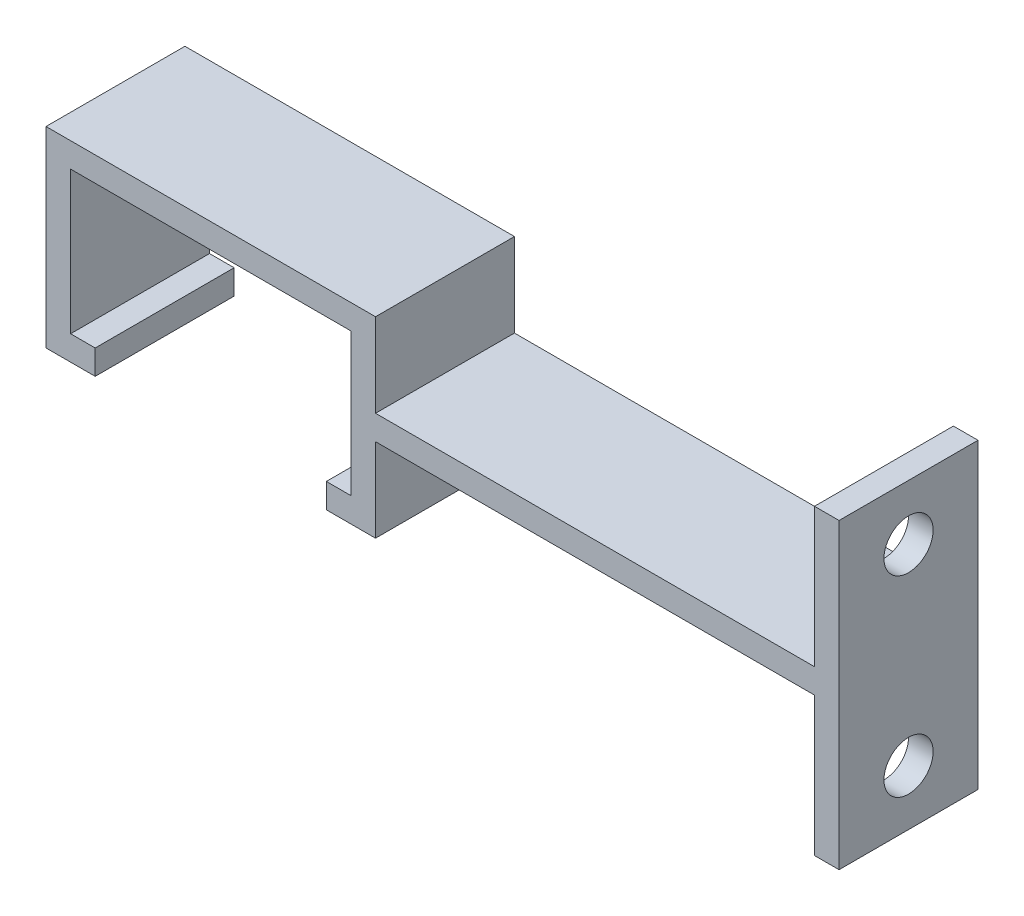
SolidWorks part; units mm, degrees
material "PLA"
ref_plane "Plan de face" through (0, 0, 0) normal (0, 0, 1) x (1, 0, 0)
ref_plane "Plan de dessus" through (0, 0, 0) normal (0, 1, 0) x (1, 0, 0)
ref_plane "Plan de droite" through (0, 0, 0) normal (1, 0, 0) x (0, 0, -1)
sketch "Esquisse1" plane through (0, 0, 0) normal (0, 0, 1) x (1, 0, 0)
  line L0 (-21.8, 1) -> (-21.8, 0)
  line L1 (0, 0) -> (-3, 0)
  line L2 (0, 0) -> (0, 13.6)
  line L3 (0, 13.6) -> (-24.8, 13.6)
  line L4 (-24.8, 0) -> (-24.8, 13.6)
  line L5 (-23.8, 12.6) -> (-1, 12.6)
  line L6 (-23.8, 12.6) -> (-23.8, 1)
  line L7 (-23.8, 1) -> (-21.8, 1)
  line L8 (-1, 12.6) -> (-1, 1)
  line L9 (-3, 1) -> (-3, 0)
  line L10 (-3, 1) -> (-1, 1)
  line L11 (-21.8, 0) -> (-24.8, 0)
  dimension "D1" = 13.6
  dimension "D2" = 24.8
  dimension "D3" = 1
  dimension "D4" = 1
  dimension "D5" = 1
  dimension "D6" = 1
  dimension "D7" = 3
  dimension "D8" = 3
extrude "Boss.-Extru.1" add sketch "Esquisse1" along normal blind 11.3
sketch "Esquisse2" plane through (0, 13.6, 0) normal (0, 1, 0) x (1, 0, 0)
  line L0 (0, -11.3) -> (-24.8, -11.3) construction
  line L1 (-16.8, 0) -> (-8, 0)
  line L2 (-16.8, 0) -> (-16.8, -11.3)
  line L3 (-16.8, -11.3) -> (-8, -11.3)
  line L4 (-8, 0) -> (-8, -11.3)
  line L5 (-24.8, -11.3) -> (-24.8, 0) construction
  line L6 (0, -11.3) -> (0, 0) construction
  dimension "D1" = 8
  dimension "D2" = 8
  dimension "D3" = 11.3
extrude "Boss.-Extru.2" add sketch "Esquisse2" along normal blind 1
sketch "Esquisse8" plane through (-8, 0, 0) normal (1, 0, 0) x (0, 0, -1)
  line L1 (-11.3, 13.6) -> (0, 13.6)
  line L2 (-11.3, 13.6) -> (-11.3, 14.6)
  line L3 (-11.3, 14.6) -> (0, 14.6)
  line L4 (0, 13.6) -> (0, 14.6)
  dimension "D1" = 11.3
extrude "Boss.-Extru.5" add sketch "Esquisse8" along normal blind 10
sketch "Esquisse9" plane through (0, 13.6, 0) normal (0, -1, 0) x (1, 0, 0)
  line L1 (2, 11.3) -> (0, 11.3)
  line L2 (2, 11.3) -> (2, 0)
  line L3 (2, 0) -> (0, 0)
  line L4 (0, 11.3) -> (0, 0)
extrude "Boss.-Extru.6" add sketch "Esquisse9" along normal blind 7.8
sketch "Esquisse10" plane through (2, 0, 0) normal (1, 0, 0) x (0, 0, -1)
  line L0 (0, 5.8) -> (0, 0) construction
  line L1 (-11.3, 5.8) -> (0, 5.8)
  line L2 (-11.3, 5.8) -> (-11.3, 7.8)
  line L3 (-11.3, 7.8) -> (0, 7.8)
  line L4 (0, 5.8) -> (0, 7.8)
  dimension "D1" = 2
extrude "Boss.-Extru.7" add sketch "Esquisse10" along normal blind 36.7
sketch "Esquisse11" plane through (0, 5.8, 0) normal (0, -1, 0) x (1, 0, 0)
  line L0 (38.7, 11.3) -> (0, 11.3) construction
  line L1 (38.7, 0) -> (36.7, 0)
  line L2 (38.7, 0) -> (38.7, 11.3)
  line L3 (38.7, 11.3) -> (36.7, 11.3)
  line L4 (36.7, 0) -> (36.7, 11.3)
  dimension "D1" = 2
extrude "Boss.-Extru.8" add sketch "Esquisse11" along normal blind 11.3
sketch "Esquisse12" plane through (0, 7.8, 0) normal (0, 1, 0) x (1, 0, 0)
  line L0 (38.7, 0) -> (2, 0) construction
  line L1 (38.7, -11.3) -> (36.7, -11.3)
  line L2 (38.7, -11.3) -> (38.7, 0)
  line L3 (38.7, 0) -> (36.7, 0)
  line L4 (36.7, -11.3) -> (36.7, 0)
  dimension "D1" = 2
extrude "Boss.-Extru.9" add sketch "Esquisse12" along normal blind 11.3
sketch "Esquisse13" plane through (0, 0, 11.3) normal (0, 0, 1) x (1, 0, 0)
  line L0 (-16.8, 14.6) -> (-25.8, 14.6)
  line L1 (-25.8, 14.6) -> (-25.8, 0)
  line L2 (-25.8, 0) -> (-24.8, 0)
  line L3 (-24.8, 13.6) -> (-24.8, 0) construction
  line L4 (-16.8, 13.6) -> (-24.8, 13.6) construction
  line L6 (-24.8, 0) -> (-24.8, 13.6)
  line L7 (-24.8, 13.6) -> (-16.8, 13.6)
  line L8 (-16.8, 13.6) -> (-16.8, 14.6)
  dimension "D1" = 1
  dimension "D2" = 1
extrude "Boss.-Extru.10" add sketch "Esquisse13" against normal up to vertex (11.3 mm away)
sketch "Esquisse14" plane through (0, 5.8, 0) normal (0, -1, 0) x (1, 0, 0)
  line L0 (0, 11.3) -> (1, 11.3)
  line L1 (36.7, 11.3) -> (0, 11.3) construction
  line L2 (1, 11.3) -> (1, 0)
  line L3 (0, 0) -> (36.7, 0) construction
  line L4 (1, 0) -> (0, 0)
  line L5 (0, 0) -> (0, 11.3)
  dimension "D1" = 1
extrude "Boss.-Extru.11" add sketch "Esquisse14" along normal up to vertex
sketch "Esquisse16" plane through (2, 0, 0) normal (1, 0, 0) x (0, 0, -1)
  line L0 (-11.3, 14.6) -> (0, 14.6)
  line L1 (0, 14.6) -> (0, 7.8)
  line L2 (0, 7.8) -> (-11.3, 7.8)
  line L3 (-11.3, 7.8) -> (-11.3, 14.6)
extrude "Enlèv. mat.-Extru.1" cut sketch "Esquisse16" against normal blind 1
sketch "Esquisse19" plane through (38.7, 0, 0) normal (1, 0, 0) x (0, 0, -1)
  line L1 (-11.3, 19.1) -> (-11.3, -5.5) construction
  line L2 (-11.3, 19.1) -> (0, 19.1) construction
  line L3 (-11.3, 6.8) -> (0, 6.8) construction
  line L4 (0, -5.5) -> (0, 19.1) construction
  line L5 (0, -5.5) -> (-11.3, -5.5) construction
  circle A0 centre (-5.65, 14.6) radius 2
  circle A1 centre (-5.65, -1) radius 2
  dimension "D1" = 4
  dimension "D4" = 5.65
  dimension "D5" = 4
  dimension "D2" = 4.5
  dimension "D3" = 4.5
  dimension "D6" = 5.65
extrude "Enlèv. mat.-Extru.3" cut sketch "Esquisse19" against normal blind 10
sketch "Esquisse22" plane through (0, 0, 11.3) normal (0, 0, 1) x (1, 0, 0)
  line L0 (-25.8, 0) -> (-25.8, -1)
  line L3 (1, 0) -> (-3, 0)
  line L4 (1, 0) -> (1, -1)
  line L5 (1, -1) -> (-3, -1)
  line L6 (-21.8, 0) -> (-21.8, -1)
  line L7 (-3, 0) -> (-3, -1)
  line L8 (-21.8, 0) -> (-25.8, 0)
  line L9 (-21.8, -1) -> (-25.8, -1)
  dimension "D1" = 1
extrude "Boss.-Extru.12" add sketch "Esquisse22" against normal up to vertex (11.3 mm away)
